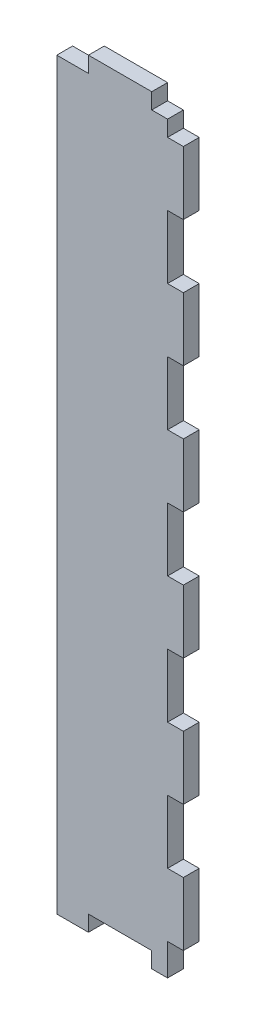
SolidWorks part; units mm, degrees
ref_plane "Front Plane" through (0, 0, 0) normal (0, 0, 1) x (1, 0, 0)
ref_plane "Top Plane" through (0, 0, 0) normal (0, 1, 0) x (1, 0, 0)
ref_plane "Right Plane" through (0, 0, 0) normal (1, 0, 0) x (0, 0, -1)
sketch "Sketch1" plane through (0, 0, 0) normal (0, 0, 1) x (1, 0, 0)
  line L1 (0, 0) -> (25.4, 0)
  line L2 (0, 0) -> (0, 152.4)
  line L3 (0, 152.4) -> (25.4, 152.4)
  line L4 (25.4, 0) -> (25.4, 152.4)
  dimension "D1" = 152.4
  dimension "D2" = 25.4
extrude "Extrude1" add sketch "Sketch1" along normal blind 3.175
sketch "Sketch3" plane through (0, 0, 3.175) normal (0, 0, 1) x (1, 0, 0)
  line L0 (25.4, 0) -> (25.4, 152.4) construction
  line L1 (25.4, 146.05) -> (22.225, 146.05)
  line L2 (25.4, 146.05) -> (25.4, 152.4)
  line L3 (25.4, 152.4) -> (22.225, 152.4)
  line L4 (22.225, 146.05) -> (22.225, 152.4)
  dimension "D1" = 6.35
  dimension "D2" = 3.175
  dimension "D3" = 6.35
extrude "Cut-Extrude1" cut sketch "Sketch3" against normal blind 3.175
pattern_linear "LPattern1" count 2 spacing 146.05 along (0, -1, 0) of "Cut-Extrude1"
sketch "Sketch4" plane through (0, 0, 3.175) normal (0, 0, 1) x (1, 0, 0)
  line L0 (25.4, 6.35) -> (25.4, 146.05) construction
  line L1 (25.4, 133.35) -> (22.225, 133.35)
  line L2 (25.4, 133.35) -> (25.4, 120.65)
  line L3 (25.4, 120.65) -> (22.225, 120.65)
  line L4 (22.225, 133.35) -> (22.225, 120.65)
  line L5 (22.225, 152.4) -> (0, 152.4) construction
  dimension "D1" = 12.7
  dimension "D2" = 3.175
  dimension "D3" = 19.05
extrude "Cut-Extrude2" cut sketch "Sketch4" against normal blind 3.175
pattern_linear "LPattern2" count 5 spacing 25.4 along (0, -1, 0) of "Cut-Extrude2"
sketch "Sketch5" plane through (0, 0, 3.175) normal (0, 0, 1) x (1, 0, 0)
  line L0 (0, 0) -> (22.225, 0) construction
  line L1 (19.05, 0) -> (6.35, 0)
  line L2 (19.05, 0) -> (19.05, 3.175)
  line L3 (19.05, 3.175) -> (6.35, 3.175)
  line L4 (6.35, 0) -> (6.35, 3.175)
  dimension "D1" = 6.35
  dimension "D2" = 12.7
  dimension "D3" = 3.175
extrude "Cut-Extrude3" cut sketch "Sketch5" against normal blind 3.175
sketch "Sketch6" plane through (0, 0, 3.175) normal (0, 0, 1) x (1, 0, 0)
  line L1 (0, 152.4) -> (6.35, 152.4)
  line L2 (0, 152.4) -> (0, 149.225)
  line L3 (0, 149.225) -> (6.35, 149.225)
  line L4 (6.35, 152.4) -> (6.35, 149.225)
  dimension "D1" = 6.35
  dimension "D2" = 3.175
extrude "Cut-Extrude4" cut sketch "Sketch6" against normal blind 3.175
pattern_linear "LPattern3" count 2 spacing 19.05 along (1, 0, 0) of "Cut-Extrude4"
